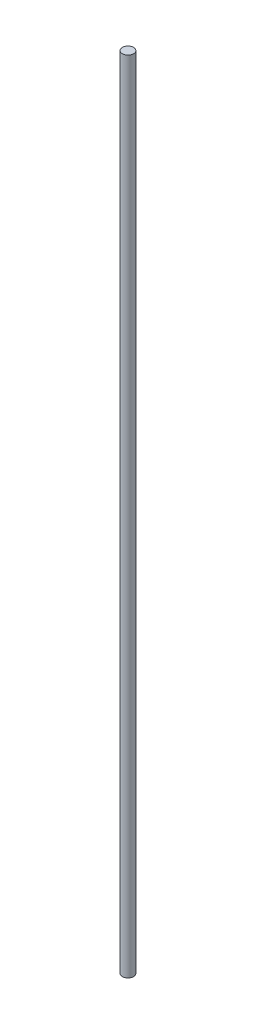
SolidWorks part; units mm, degrees
ref_plane "Front Plane" through (0, 0, 0) normal (0, 0, 1) x (1, 0, 0)
ref_plane "Top Plane" through (0, 0, 0) normal (0, 1, 0) x (1, 0, 0)
ref_plane "Right Plane" through (0, 0, 0) normal (1, 0, 0) x (0, 0, -1)
sketch "Sketch1" plane through (0, 0, 0) normal (0, 1, 0) x (1, 0, 0)
  circle A0 centre (0, 0) radius 2.5
  dimension "D1" = 5
extrude "Boss-Extrude1" add sketch "Sketch1" along normal blind 358.5
